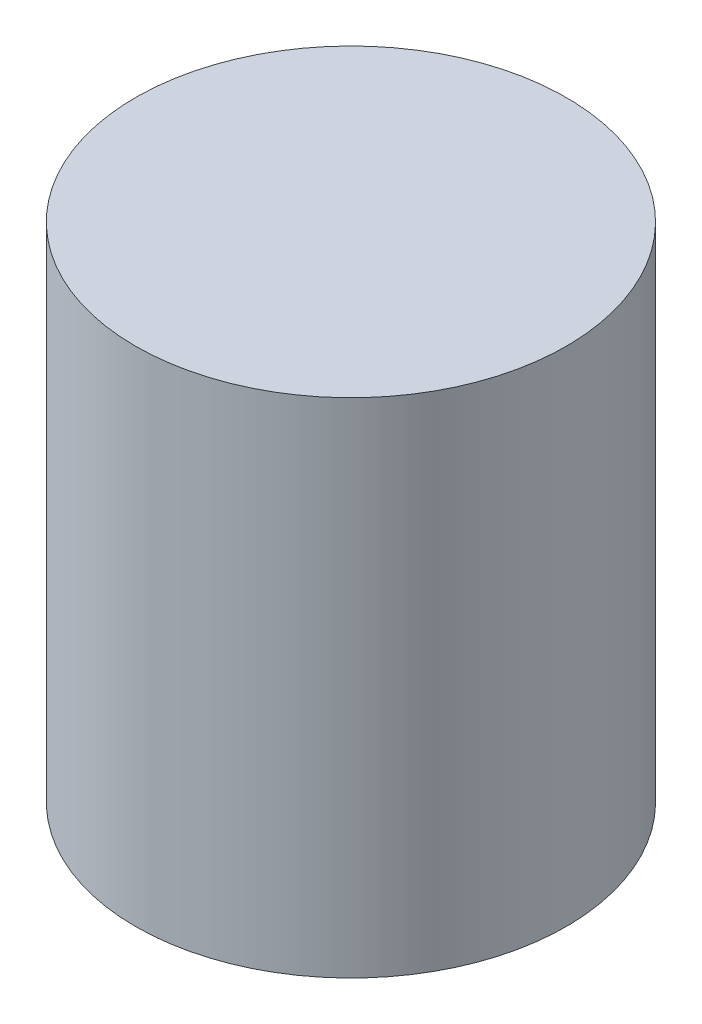
SolidWorks part; units mm, degrees
ref_plane "Спереди" through (0, 0, 0) normal (0, 0, 1) x (1, 0, 0)
ref_plane "Сверху" through (0, 0, 0) normal (0, 1, 0) x (1, 0, 0)
ref_plane "Справа" through (0, 0, 0) normal (1, 0, 0) x (0, 0, -1)
sketch "Эскиз1" plane through (0, 0, 0) normal (0, 1, 0) x (1, 0, 0)
  circle A0 centre (0, 0) radius 3
  dimension "D1" = 6
extrude "Бобышка-Вытянуть1" add sketch "Эскиз1" along normal blind 7
sketch "Эскиз2" plane through (0, 0, 0) normal (0, -1, 0) x (1, 0, 0)
  line L1 (-0.5276, -3.2483) -> (2.5493, -2.0811)
  line L2 (2.5493, -2.0811) -> (3.0769, 1.1673)
  line L3 (3.0769, 1.1673) -> (0.5276, 3.2483)
  line L4 (0.5276, 3.2483) -> (-2.5493, 2.0811)
  line L5 (-2.5493, 2.0811) -> (-3.0769, -1.1673)
  line L6 (-3.0769, -1.1673) -> (-0.5276, -3.2483)
  circle A0 centre (0, 0) radius 2.85 construction
  dimension "D1" = 5.7
